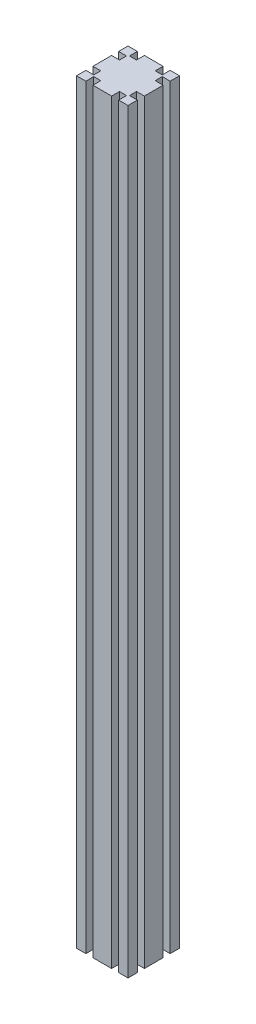
SolidWorks part; units mm, degrees
ref_plane "前视基准面" through (0, 0, 0) normal (0, 0, 1) x (1, 0, 0)
ref_plane "上视基准面" through (0, 0, 0) normal (0, 1, 0) x (1, 0, 0)
ref_plane "右视基准面" through (0, 0, 0) normal (1, 0, 0) x (0, 0, -1)
sketch "草图1" plane through (0, 0, 0) normal (0, 1, 0) x (1, 0, 0)
  line L0 (0, 60) -> (0, 49.1)
  line L1 (0, 0) -> (60, 0)
  line L2 (0, 0) -> (0, 60)
  line L3 (0, 60) -> (60, 60)
  line L4 (60, 0) -> (60, 60)
  line L5 (0, 0) -> (60, 60) construction
  line L6 (0, 60) -> (60, 0) construction
  line L7 (0, 49.1) -> (9.2, 49.1)
  line L8 (9.2, 49.1) -> (9.2, 40.9)
  line L9 (9.2, 40.9) -> (0, 40.9)
  line L10 (0, 30) -> (30, 30)
  line L11 (30, 30) -> (30, 60)
  line L12 (60, 49.1) -> (50.8, 49.1)
  line L13 (50.8, 49.1) -> (50.8, 40.9)
  line L14 (50.8, 40.9) -> (60, 40.9)
  line L15 (10.9, 0) -> (10.9, 9.2)
  line L16 (10.9, 9.2) -> (19.1, 9.2)
  line L17 (19.1, 9.2) -> (19.1, 0)
  line L18 (10.9, 50.8) -> (19.1, 50.8)
  line L19 (10.9, 60) -> (10.9, 50.8)
  line L20 (19.1, 50.8) -> (19.1, 60)
  line L21 (9.2, 19.1) -> (0, 19.1)
  line L22 (9.2, 10.9) -> (9.2, 19.1)
  line L23 (0, 10.9) -> (9.2, 10.9)
  line L24 (49.1, 60) -> (49.1, 50.8)
  line L25 (49.1, 50.8) -> (40.9, 50.8)
  line L26 (40.9, 50.8) -> (40.9, 60)
  line L27 (50.8, 19.1) -> (60, 19.1)
  line L28 (60, 10.9) -> (50.8, 10.9)
  line L29 (50.8, 10.9) -> (50.8, 19.1)
  line L30 (49.1, 9.2) -> (40.9, 9.2)
  line L31 (49.1, 0) -> (49.1, 9.2)
  line L32 (40.9, 9.2) -> (40.9, 0)
  point P4 (30, 30)
extrude "凸台-拉伸1" add sketch "草图1" along normal blind 880 contours L20 L18 L19 L3 L0 L7 L8 L9 L2 L10 L11 | L32 L30 L31 L1 L4 L28 L29 L27 L14 L13 L12 L3 L24 L25 L26 L11 L10 L2 L21 L22 L23 L15 L16 L17
